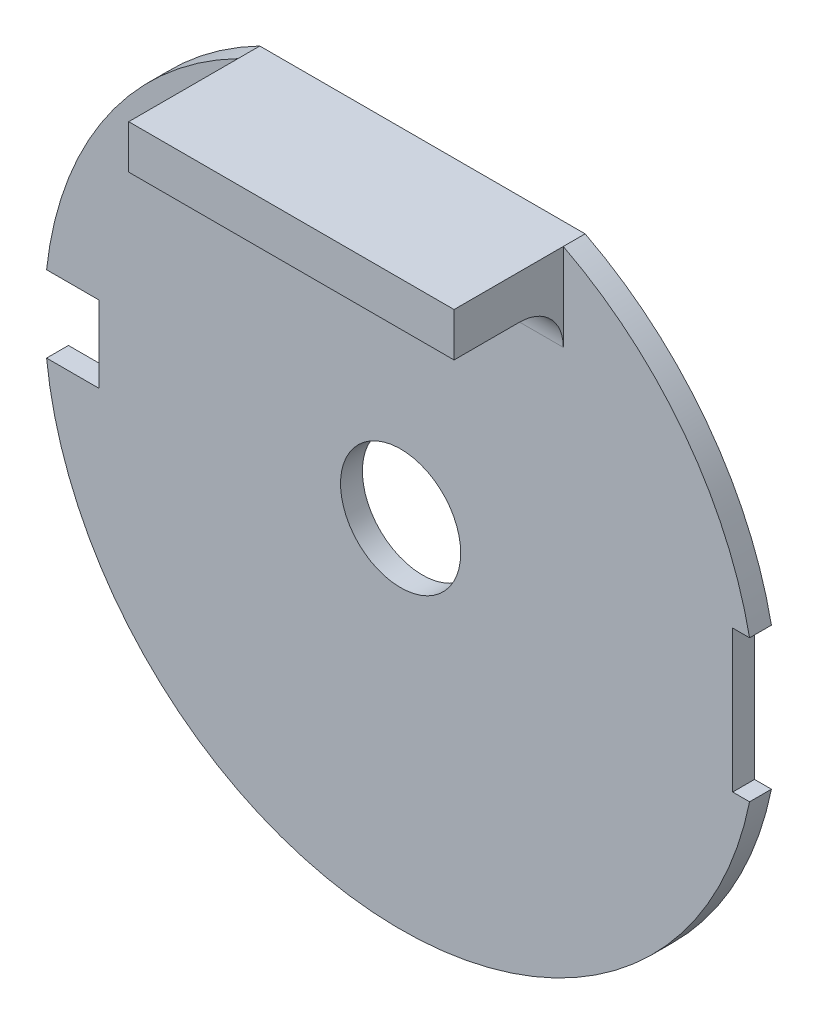
SolidWorks part; units mm, degrees
ref_plane "前视基准面" through (0, 0, 0) normal (0, 0, 1) x (1, 0, 0)
ref_plane "上视基准面" through (0, 0, 0) normal (0, 1, 0) x (1, 0, 0)
ref_plane "右视基准面" through (0, 0, 0) normal (1, 0, 0) x (0, 0, -1)
sketch "草图1" plane through (0, 0, 0) normal (0, 0, 1) x (1, 0, 0)
  line L0 (-7.4458, 14.5) -> (7.4458, 14.5)
  arc A0 (-7.4458, 14.5) -> (7.4458, 14.5) centre (0, 0) ccw
  circle A1 centre (0, 0) radius 2.75
  dimension "D1" = 32.6
  dimension "D2" = 5.5
  dimension "D3" = 14.5
extrude "凸台-拉伸1" add sketch "草图1" along normal blind 1
sketch "草图2" plane through (0, 0, 1) normal (0, 0, 1) x (1, 0, 0)
  line L0 (-13.8, 1.75) -> (15.2, 1.75) construction
  line L1 (-18.8, 1.75) -> (-13.8, 1.75)
  line L2 (-18.8, 1.75) -> (-18.8, -1.75)
  line L3 (-18.8, -1.75) -> (-13.8, -1.75)
  line L4 (-13.8, 1.75) -> (-13.8, -1.75)
  line L5 (15.2, 1.75) -> (17.8078, 1.75) construction
  line L6 (15.2, 1.75) -> (15.2, -1.75) construction
  line L7 (15.2, -1.75) -> (17.8078, -1.75) construction
  line L8 (17.8078, 1.75) -> (17.8078, -1.75) construction
  line L9 (15.2, -1.75) -> (-13.8, -1.75) construction
  line L11 (15.2, 3.25) -> (17.2, 3.25)
  line L12 (15.2, 3.25) -> (15.2, -3.25)
  line L13 (15.2, -3.25) -> (17.2, -3.25)
  line L14 (17.2, 3.25) -> (17.2, -3.25)
  circle A0 centre (0, 0) radius 16.3 construction
  point P10 (-16.3, 0)
  point P11 (16.3, 0)
  point P13 (-13.8, 0)
  point P17 (17.2, 0)
  dimension "D1" = 29
  dimension "D2" = 2.5
  dimension "D3" = 5
  dimension "D4" = 3.5
  dimension "D5" = 6.5
  dimension "D6" = 2
extrude "切除-拉伸1" cut sketch "草图2" against normal through all
sketch "草图3" plane through (0, 0, 1) normal (0, 0, 1) x (1, 0, 0)
  line L1 (-7.4458, 14.5) -> (7.4458, 14.5)
  line L2 (-7.4458, 14.5) -> (-7.4458, 12.5)
  line L3 (-7.4458, 12.5) -> (7.4458, 12.5)
  line L4 (7.4458, 14.5) -> (7.4458, 12.5)
  dimension "D1" = 2
extrude "凸台-拉伸2" add sketch "草图3" along normal blind 5
fillet "圆角1" radius 2 1 edges at (0, 12.5, 1)
